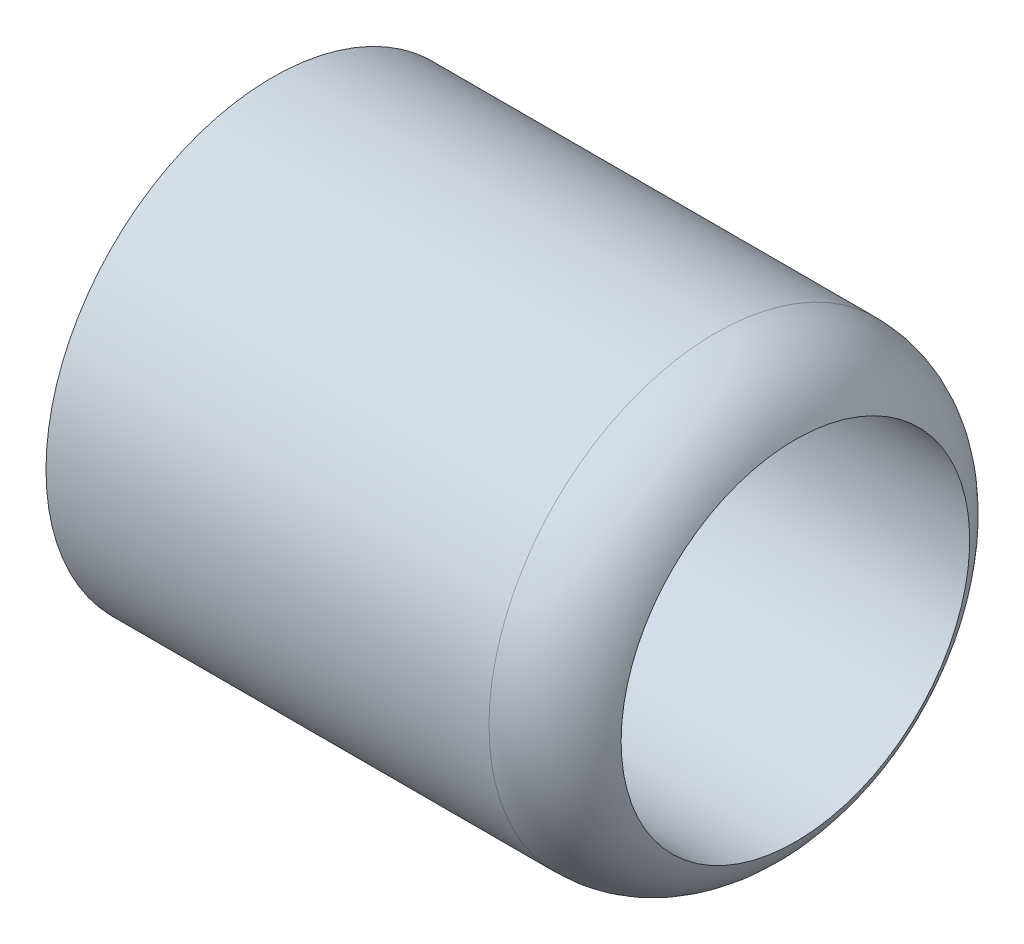
SolidWorks part; units mm, degrees
ref_plane "Front Plane" through (0, 0, 0) normal (0, 0, 1) x (1, 0, 0)
ref_plane "Top Plane" through (0, 0, 0) normal (0, 1, 0) x (1, 0, 0)
ref_plane "Right Plane" through (0, 0, 0) normal (1, 0, 0) x (0, 0, -1)
sketch "Sketch1" plane through (0, 0, 0) normal (0, 0, 1) x (1, 0, 0)
  line L0 (-29.819, -12.7) -> (37.3254, -12.7) construction
  line L1 (0, 0) -> (12.7, 0)
  line L2 (12.7, -4.572) -> (19.05, -4.572)
  line L3 (12.7, -4.572) -> (12.7, 0)
  line L4 (32.2801, 3.81) -> (0, 3.81)
  line L5 (0, 3.81) -> (0, 0)
  line L7 (19.05, 0) -> (19.05, -4.572)
  line L8 (19.05, 0) -> (38.1, 0)
  arc A0 (32.2801, 3.81) -> (38.1, 0) centre (32.2801, -2.54) cw
  dimension "D4" = 6.35
  dimension "D1" = 16.51
  dimension "D2" = 38.1
  dimension "D3" = 12.7
  dimension "D5" = 6.35
  dimension "D6" = 12.7
  dimension "D7" = 8.128
revolve "Revolve1" add sketch "Sketch1" angle 360 about L0
chamfer "Chamfer1" distance 1.524 angle 45 1 edges at (0, -12.7, 12.7)
